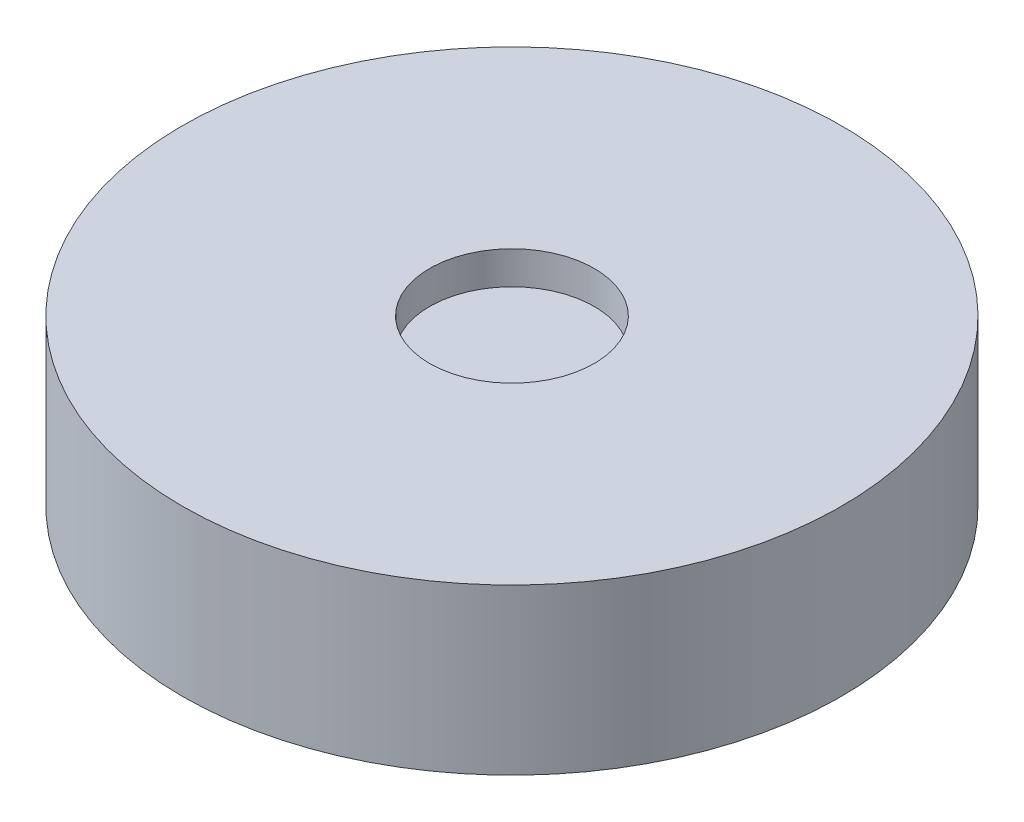
SolidWorks part; units mm, degrees
ref_plane "Front Plane" through (0, 0, 0) normal (0, 0, 1) x (1, 0, 0)
ref_plane "Top Plane" through (0, 0, 0) normal (0, 1, 0) x (1, 0, 0)
ref_plane "Right Plane" through (0, 0, 0) normal (1, 0, 0) x (0, 0, -1)
sketch "Sketch1" plane through (0, 0, 0) normal (0, 1, 0) x (1, 0, 0)
  circle A0 centre (0, 0) radius 50.8317
extrude "Boss-Extrude1" add sketch "Sketch1" along normal blind 25.4
sketch "Sketch2" plane through (0, 25.4, 0) normal (0, 1, 0) x (1, 0, 0)
  circle A0 centre (0, 0) radius 12.7
extrude "Cut-Extrude1" cut sketch "Sketch2" against normal blind 5.08
